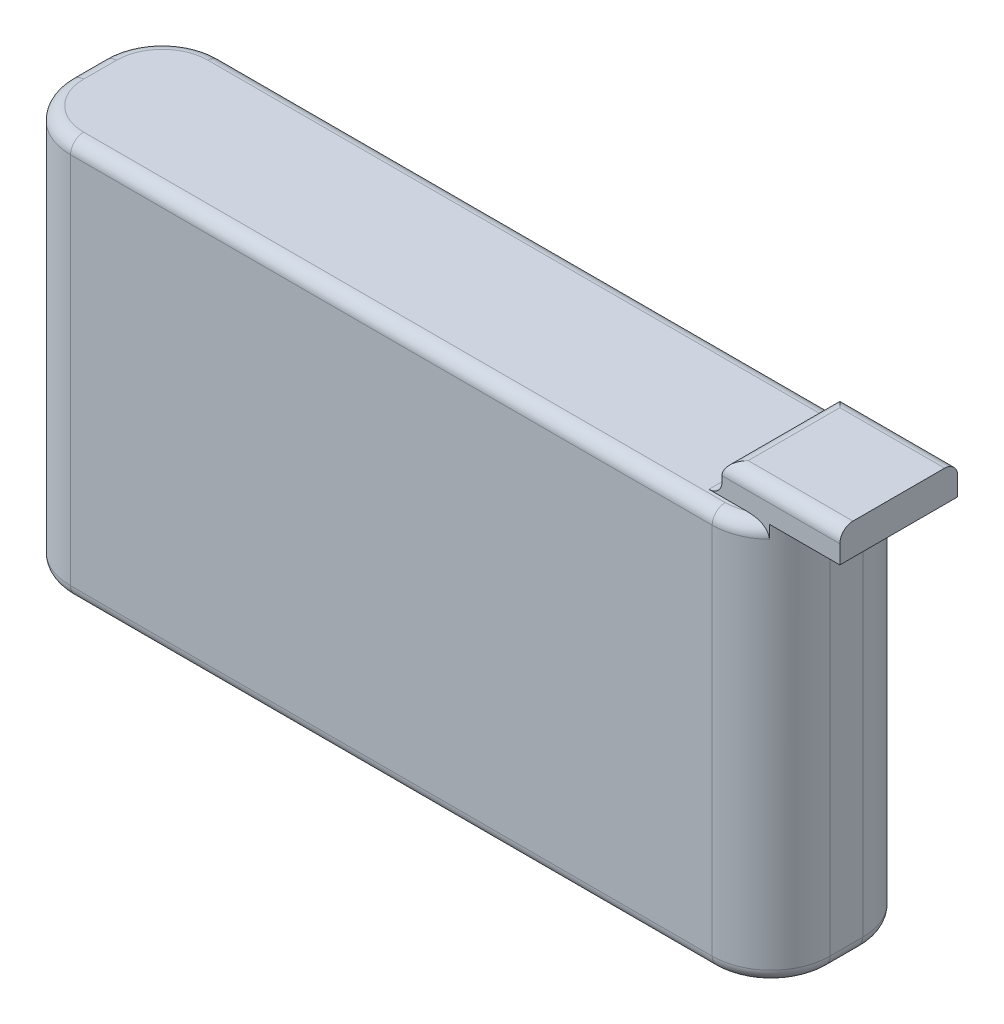
SolidWorks part; units mm, degrees
ref_plane "Front Plane" through (0, 0, 0) normal (0, 0, 1) x (1, 0, 0)
ref_plane "Top Plane" through (0, 0, 0) normal (0, 1, 0) x (1, 0, 0)
ref_plane "Right Plane" through (0, 0, 0) normal (1, 0, 0) x (0, 0, -1)
sketch "Sketch1" plane through (0, 0, 0) normal (0, 0, 1) x (1, 0, 0)
  line L1 (0, 0) -> (58, 0)
  line L2 (0, 0) -> (0, 30.5)
  line L3 (0, 30.5) -> (58, 30.5)
  line L4 (58, 0) -> (58, 30.5)
  dimension "D1" = 58
  dimension "D2" = 30.5
extrude "Boss-Extrude1" add sketch "Sketch1" along normal blind 11.5
fillet "Fillet1" radius 4.5 4 edges at (0, 15.25, 0) (0, 15.25, 11.5) (58, 15.25, 0) (58, 15.25, 11.5)
sketch "Sketch2" plane through (0, 30.5, 0) normal (0, 1, 0) x (1, 0, 0)
  line L0 (0, -7) -> (0, -4.5) construction
  line L1 (53, -10.25) -> (62, -10.25)
  line L2 (53, -10.25) -> (53, -1.25)
  line L3 (53, -1.25) -> (62, -1.25)
  line L4 (62, -10.25) -> (62, -1.25)
  line L5 (58, -7) -> (58, -4.5) construction
  point P4 (63.4244, -2.621)
  point P5 (62, -5.75)
  point P8 (0, -5.75)
  dimension "D1" = 9
  dimension "D2" = 9
  dimension "D3" = 5
extrude "Boss-Extrude2" add sketch "Sketch2" along normal blind 2.4
fillet "Fillet2" radius 1 19 edges at (1.318, 0, 1.318) (0, 0, 5.75) (1.318, 0, 10.182) (29, 0, 11.5) (56.682, 0, 10.182) (58, 0, 5.75) (56.682, 0, 1.318) (55.1771, 30.5, 0.3242) (55.1771, 30.5, 11.1758) (29, 30.5, 11.5) (1.318, 30.5, 10.182) (0, 30.5, 5.75) (1.318, 30.5, 1.318) (29, 0, 0) (57.5, 32.9, 10.25) (57.5, 32.9, 1.25) (53, 32.9, 5.75) (53, 30.5, 5.75) (29, 30.5, 0)
